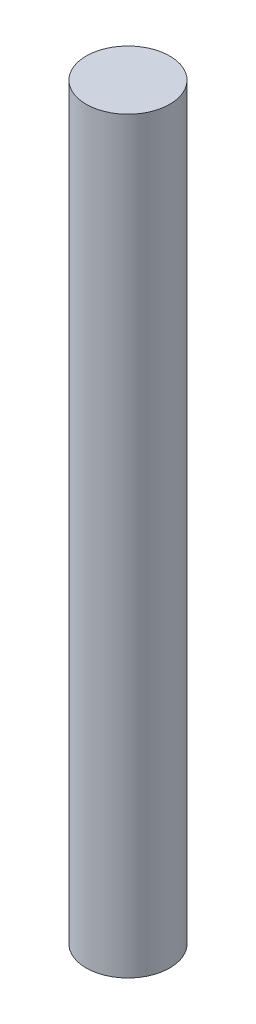
SolidWorks part; units mm, degrees
ref_plane "Front Plane" through (0, 0, 0) normal (0, 0, 1) x (1, 0, 0)
ref_plane "Top Plane" through (0, 0, 0) normal (0, 1, 0) x (1, 0, 0)
ref_plane "Right Plane" through (0, 0, 0) normal (1, 0, 0) x (0, 0, -1)
sketch "Sketch1" plane through (0, 0, 0) normal (0, 1, 0) x (1, 0, 0)
  circle A0 centre (0, 0) radius 5.588
  dimension "D1" = 11.176
extrude "Boss-Extrude1" add sketch "Sketch1" along normal blind 100
